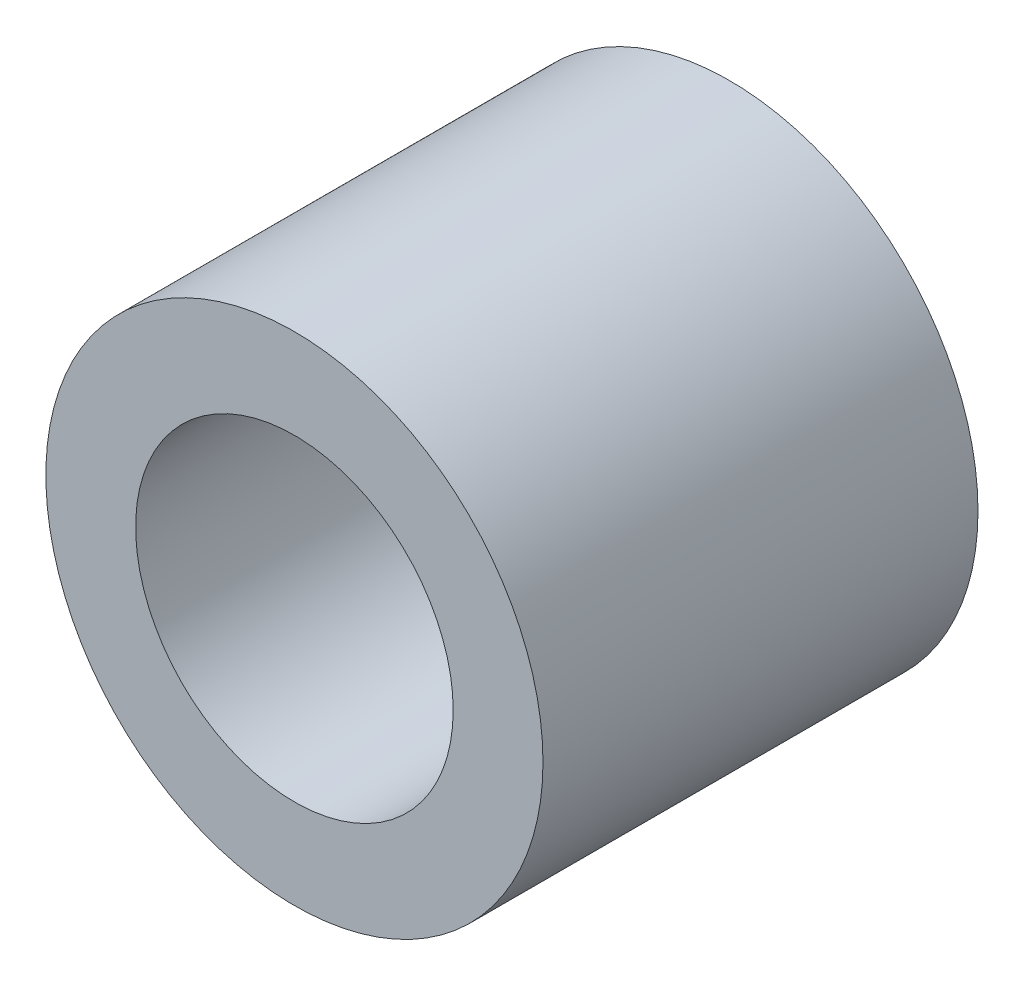
SolidWorks part; units mm, degrees
material "ABS"
ref_plane "Front Plane" through (0, 0, 0) normal (0, 0, 1) x (1, 0, 0)
ref_plane "Top Plane" through (0, 0, 0) normal (0, 1, 0) x (1, 0, 0)
ref_plane "Right Plane" through (0, 0, 0) normal (1, 0, 0) x (0, 0, -1)
sketch "Sketch1" plane through (0, 0, 0) normal (0, 0, 1) x (1, 0, 0)
  circle A0 centre (0, 0) radius 4
  circle A1 centre (0, 0) radius 2.555
  dimension "D1" = 8
  dimension "D2" = 5.11
extrude "Boss-Extrude1" add sketch "Sketch1" along normal blind 7
cosmetic thread "Cosmetic Thread1" parameters "D2"=6.35
